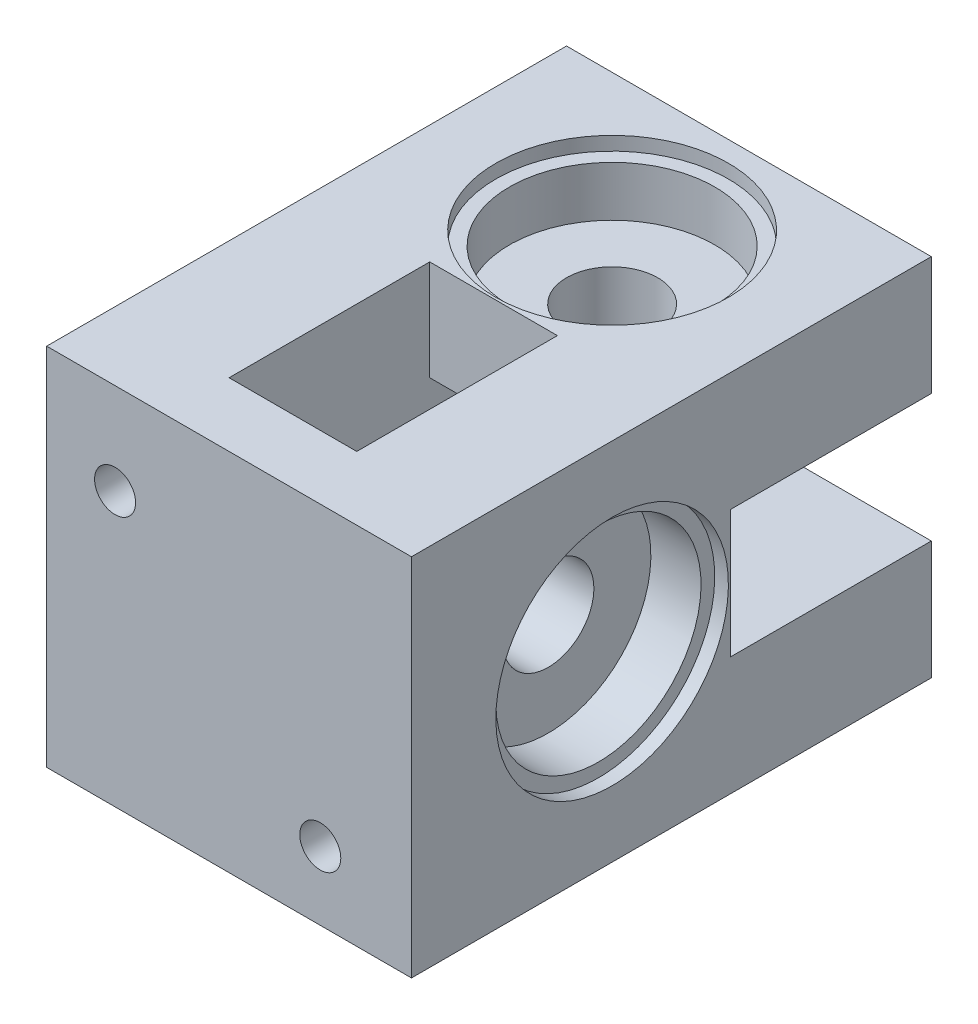
SolidWorks part; units mm, degrees
ref_plane "Plan de face" through (0, 0, 0) normal (0, 0, 1) x (1, 0, 0)
ref_plane "Plan de dessus" through (0, 0, 0) normal (0, 1, 0) x (1, 0, 0)
ref_plane "Plan de droite" through (0, 0, 0) normal (1, 0, 0) x (0, 0, -1)
sketch "Esquisse1" plane through (0, 0, 0) normal (0, 0, 1) x (1, 0, 0)
  line L1 (-40, 40) -> (0, 40)
  line L2 (-40, 40) -> (-40, 0)
  line L3 (-40, 0) -> (0, 0)
  line L4 (0, 40) -> (0, 0)
  dimension "D1" = 40
  dimension "D2" = 40
extrude "Boss.-Extru.1" add sketch "Esquisse1" along normal blind 50
sketch "Esquisse2" plane through (0, 40, 0) normal (0, 1, 0) x (1, 0, 0)
  line L0 (0, 0) -> (-40, 0) construction
  line L1 (-40, -50) -> (-40, 0) construction
  circle A0 centre (-20, -15) radius 5
  dimension "D1" = 10
  dimension "D2" = 15
  dimension "D3" = 20
extrude "Enlèv. mat.-Extru.1" cut sketch "Esquisse2" against normal through all
sketch "Esquisse3" plane through (-40, 0, 0) normal (-1, 0, 0) x (0, 0, 1)
  line L0 (50, 40) -> (50, 0) construction
  line L1 (50, 40) -> (0, 40) construction
  circle A0 centre (35, 20) radius 5
  dimension "D1" = 10
  dimension "D2" = 15
  dimension "D3" = 20
extrude "Enlèv. mat.-Extru.2" cut sketch "Esquisse3" against normal through all
sketch "Esquisse4" plane through (-40, 0, 0) normal (-1, 0, 0) x (0, 0, 1)
  line L1 (25, 27) -> (5, 27)
  line L2 (25, 27) -> (25, 13)
  line L3 (25, 13) -> (5, 13)
  line L4 (5, 27) -> (5, 13)
  line L5 (0, 40) -> (0, 0) construction
  line L6 (50, 0) -> (0, 0) construction
  line L7 (50, 40) -> (0, 40) construction
  dimension "D1" = 14
  dimension "D2" = 20
  dimension "D3" = 5
  dimension "D4" = 13
  dimension "D5" = 13
extrude "Enlèv. mat.-Extru.3" cut sketch "Esquisse4" against normal blind 29
sketch "Esquisse5" plane through (0, 0, 0) normal (0, -1, 0) x (1, 0, 0)
  line L0 (-40, 50) -> (0, 50) construction
  line L1 (-13, 25) -> (-27, 25)
  line L2 (-13, 25) -> (-13, 45)
  line L3 (-13, 45) -> (-27, 45)
  line L4 (-27, 25) -> (-27, 45)
  line L5 (-40, 50) -> (-40, 0) construction
  dimension "D1" = 20
  dimension "D2" = 5
  dimension "D3" = 14
  dimension "D4" = 13
extrude "Enlèv. mat.-Extru.4" cut sketch "Esquisse5" against normal blind 29
sketch "Esquisse6" plane through (0, 0, 0) normal (1, 0, 0) x (0, 0, -1)
  line L0 (0, 0) -> (0, 40) construction
  line L1 (0, 27) -> (-22, 27)
  line L2 (0, 27) -> (0, 13)
  line L3 (0, 13) -> (-22, 13)
  line L4 (-22, 27) -> (-22, 13)
  line L5 (-50, 0) -> (0, 0) construction
  dimension "D1" = 14
  dimension "D2" = 22
  dimension "D3" = 13
extrude "Enlèv. mat.-Extru.5" cut sketch "Esquisse6" against normal blind 24
sketch "Esquisse7" plane through (0, 40, 0) normal (0, 1, 0) x (1, 0, 0)
  line L0 (0, -50) -> (-40, -50) construction
  line L1 (-27, -50) -> (-13, -50)
  line L2 (-27, -50) -> (-27, -28)
  line L3 (-27, -28) -> (-13, -28)
  line L4 (-13, -50) -> (-13, -28)
  line L5 (-40, -50) -> (-40, 0) construction
  dimension "D1" = 14
  dimension "D2" = 22
  dimension "D3" = 13
extrude "Enlèv. mat.-Extru.6" cut sketch "Esquisse7" against normal blind 24
sketch "Esquisse8" plane through (0, 0, 0) normal (1, 0, 0) x (0, 0, -1)
  circle A0 centre (-35, 20) radius 11.25
  dimension "D1" = 22.5
extrude "Enlèv. mat.-Extru.7" cut sketch "Esquisse8" against normal blind 7
sketch "Esquisse9" plane through (0, 0, 0) normal (1, 0, 0) x (0, 0, -1)
  circle A0 centre (-35, 20) radius 12.75
  dimension "D1" = 25.5
extrude "Enlèv. mat.-Extru.8" cut sketch "Esquisse9" against normal blind 1.5
sketch "Esquisse10" plane through (0, 40, 0) normal (0, 1, 0) x (1, 0, 0)
  circle A0 centre (-20, -15) radius 11.25
  dimension "D1" = 22.5
extrude "Enlèv. mat.-Extru.9" cut sketch "Esquisse10" against normal blind 7
sketch "Esquisse11" plane through (0, 40, 0) normal (0, 1, 0) x (1, 0, 0)
  circle A0 centre (-20, -15) radius 12.75
  dimension "D1" = 25.5
extrude "Enlèv. mat.-Extru.10" cut sketch "Esquisse11" against normal blind 1.5
sketch "Esquisse12" plane through (0, 0, 50) normal (0, 0, 1) x (1, 0, 0)
  line L1 (0, 40) -> (-40, 40)
  line L2 (0, 40) -> (0, 0)
  line L3 (0, 0) -> (-40, 0)
  line L4 (-40, 40) -> (-40, 0)
extrude "Boss.-Extru.2" add sketch "Esquisse12" along normal blind 7
sketch "Esquisse13" plane through (0, 0, 57) normal (0, 0, 1) x (1, 0, 0)
  line L0 (0, 0) -> (0, 40) construction
  line L1 (0, 40) -> (-40, 40) construction
  circle A0 centre (-32.5, 30) radius 2.25
  circle A1 centre (-10, 7.5) radius 2.25
  dimension "D1" = 4.5
  dimension "D2" = 32.5
  dimension "D3" = 4.5
  dimension "D4" = 32.5
  dimension "D5" = 10
  dimension "D6" = 10
extrude "Enlèv. mat.-Extru.11" cut sketch "Esquisse13" against normal blind 15
sketch "Esquisse14" plane through (0, 0, 0) normal (0, -1, 0) x (1, 0, 0)
  line L0 (-40, 57) -> (0, 57) construction
  line L1 (-6.25, 49.5) -> (-13.75, 49.5)
  line L2 (-6.25, 49.5) -> (-6.25, 53)
  line L3 (-6.25, 53) -> (-13.75, 53)
  line L4 (-13.75, 49.5) -> (-13.75, 53)
  line L5 (0, 57) -> (0, 0) construction
  dimension "D1" = 7.5
  dimension "D2" = 3.5
  dimension "D3" = 4
  dimension "D4" = 6.25
extrude "Enlèv. mat.-Extru.12" cut sketch "Esquisse14" against normal blind 12
sketch "Esquisse15" plane through (-40, 0, 0) normal (-1, 0, 0) x (0, 0, 1)
  line L0 (57, 40) -> (57, 0) construction
  line L1 (49.5, 26.25) -> (53, 26.25)
  line L2 (49.5, 26.25) -> (49.5, 33.75)
  line L3 (49.5, 33.75) -> (53, 33.75)
  line L4 (53, 26.25) -> (53, 33.75)
  line L5 (57, 40) -> (0, 40) construction
  dimension "D1" = 7.5
  dimension "D2" = 3.5
  dimension "D3" = 4
  dimension "D4" = 6.25
extrude "Enlèv. mat.-Extru.13" cut sketch "Esquisse15" against normal blind 12
